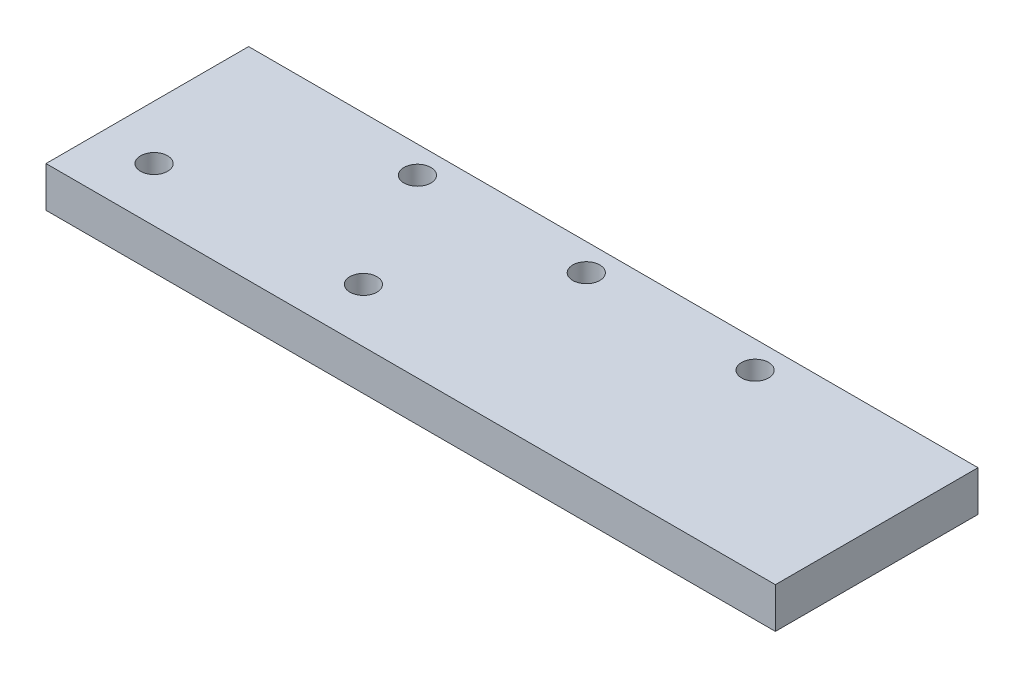
SolidWorks part; units mm, degrees
ref_plane "Front Plane" through (0, 0, 0) normal (0, 0, 1) x (1, 0, 0)
ref_plane "Top Plane" through (0, 0, 0) normal (0, 1, 0) x (1, 0, 0)
ref_plane "Right Plane" through (0, 0, 0) normal (1, 0, 0) x (0, 0, -1)
sketch "Sketch1" plane through (0, 0, 0) normal (0, 1, 0) x (1, 0, 0)
  line L1 (-102.5105, 65.1674) -> (5.4895, 65.1674)
  line L2 (-102.5105, 65.1674) -> (-102.5105, 35.1674)
  line L3 (-102.5105, 35.1674) -> (5.4895, 35.1674)
  line L4 (5.4895, 65.1674) -> (5.4895, 35.1674)
  dimension "D1" = 30
  dimension "D2" = 108
extrude "Boss-Extrude1" add sketch "Sketch1" along normal blind 6 contours L2 L3 L4 L1
sketch "Sketch2" plane through (0, 0, 0) normal (0, -1, 0) x (1, 0, 0)
  line L0 (-102.5105, -65.1674) -> (-102.5105, -35.1674) construction
  line L1 (-102.5105, -65.1674) -> (5.4895, -65.1674) construction
  line L2 (5.4895, -65.1674) -> (5.4895, -35.1674) construction
  line L3 (-102.5105, -35.1674) -> (5.4895, -35.1674) construction
  circle A0 centre (-73.5105, -61.1674) radius 2
  circle A1 centre (-48.5105, -61.1674) radius 2
  circle A2 centre (-23.5105, -61.1674) radius 2
  circle A3 centre (-94.5105, -43.1674) radius 2
  circle A4 centre (-63.5105, -43.1674) radius 2
  dimension "D1" = 29
  dimension "D5" = 25
  dimension "D7" = 31
  dimension "D2" = 4
  dimension "D3" = 25
  dimension "D4" = 4
  dimension "D6" = 4
  dimension "D8" = 8
  dimension "D9" = 8
  dimension "D10" = 8
extrude "Cut-Extrude1" cut sketch "Sketch2" against normal blind 10
